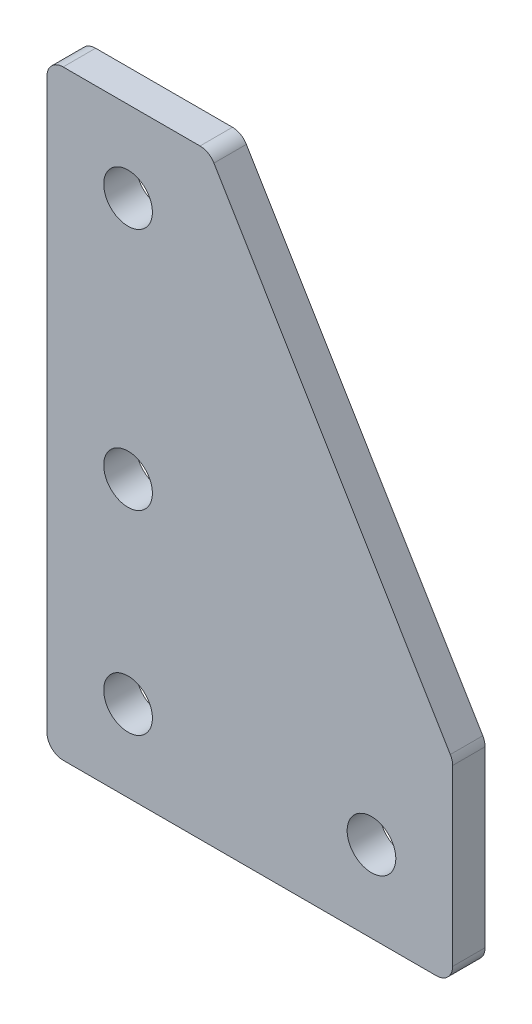
SolidWorks part; units mm, degrees
material "环氧板3240"
ref_plane "前视基准面" through (0, 0, 0) normal (0, 0, 1) x (1, 0, 0)
ref_plane "上视基准面" through (0, 0, 0) normal (0, 1, 0) x (1, 0, 0)
ref_plane "右视基准面" through (0, 0, 0) normal (1, 0, 0) x (0, 0, -1)
other "Configuration Table"
sketch "草图1" plane through (0, 0, 0) normal (0, 0, 1) x (1, 0, 0)
  line L0 (-5, 32) -> (5, 32)
  line L1 (5, 32) -> (20, 7)
  line L2 (20, 7) -> (20, -5)
  line L3 (20, -5) -> (-5, -5)
  line L4 (-5, -5) -> (-5, 32)
  line L5 (0, 32) -> (0, -5) construction
  line L6 (20, 7) -> (-5, 7) construction
  line L7 (20, 0) -> (-5, 0) construction
  circle A0 centre (0, 27) radius 1.5
  circle A1 centre (0, 12) radius 1.5
  circle A2 centre (15, 0) radius 1.5
  circle A3 centre (0, 0) radius 1.5
  point P17 (20, 0)
  point P19 (0, 0)
  point P20 (-5, 0)
  dimension "D3" = 3
  dimension "D5" = 15
  dimension "D6" = 15
  dimension "D7" = 5
  dimension "D1" = 12
  dimension "D2" = 10
  dimension "D4" = 5
  dimension "D8" = 5
  dimension "D9" = 5
extrude "凸台-拉伸1" add sketch "草图1" along normal blind 2
fillet "圆角1" radius 1 5 edges at (20, -5, 1) (-5, -5, 1) (20, 7, 1) (5, 32, 1) (-5, 32, 1)
